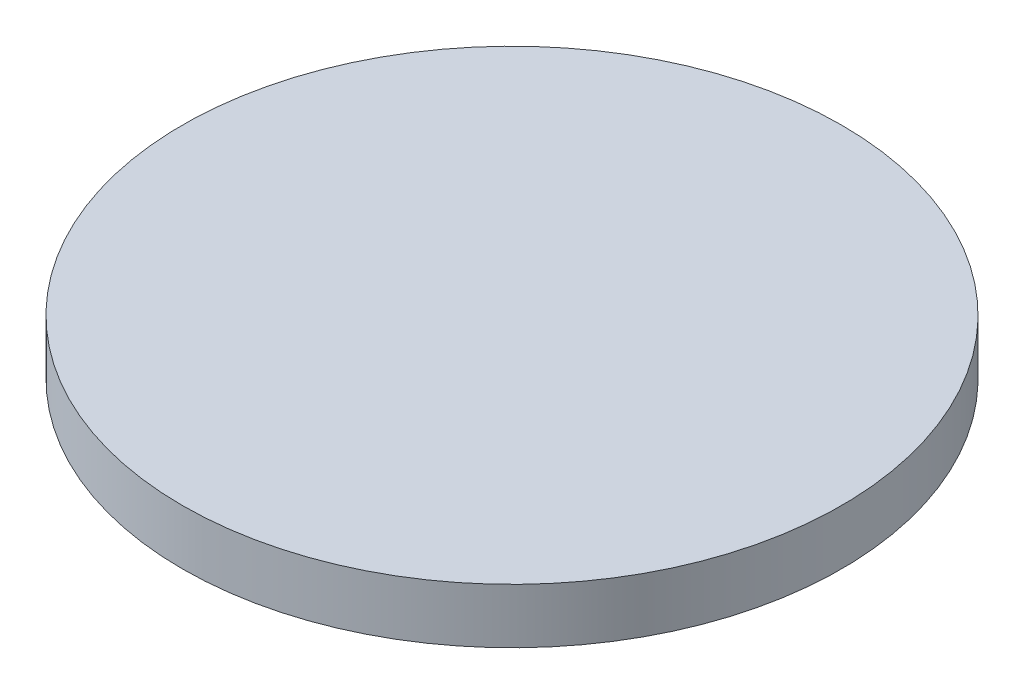
SolidWorks part; units mm, degrees
ref_plane "Plan de face" through (0, 0, 0) normal (0, 0, 1) x (1, 0, 0)
ref_plane "Plan de dessus" through (0, 0, 0) normal (0, 1, 0) x (1, 0, 0)
ref_plane "Plan de droite" through (0, 0, 0) normal (1, 0, 0) x (0, 0, -1)
sketch "Esquisse1" plane through (0, 0, 0) normal (0, 0, 1) x (1, 0, 0)
  line L0 (0, 5.1405) -> (0, -3.9174) construction
  line L1 (0, 0) -> (0, 2)
  line L2 (0, 2) -> (12, 2)
  line L3 (12, 2) -> (12, 0)
  line L4 (12, 0) -> (0, 0)
  dimension "D1" = 2
  dimension "D2" = 12
revolve "Révolution1" add sketch "Esquisse1" angle 360 about L0
